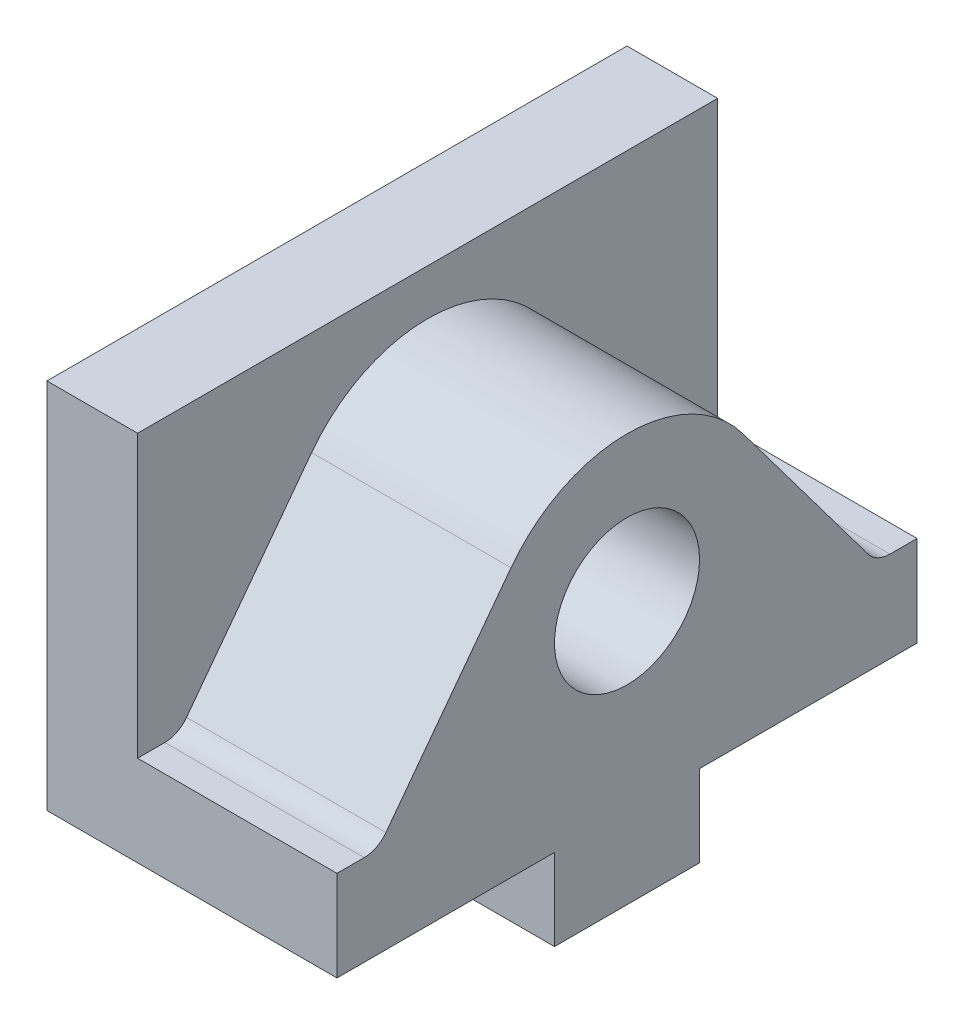
SolidWorks part; units mm, degrees
ref_plane "Front Plane" through (0, 0, 0) normal (0, 0, 1) x (1, 0, 0)
ref_plane "Top Plane" through (0, 0, 0) normal (0, 1, 0) x (1, 0, 0)
ref_plane "Right Plane" through (0, 0, 0) normal (1, 0, 0) x (0, 0, -1)
sketch "Sketch1" plane through (0, 0, 0) normal (1, 0, 0) x (0, 0, -1)
  line L0 (-32, -8) -> (32, -8)
  line L1 (-32, 18) -> (32, 18)
  line L2 (-32, 18) -> (-32, -18)
  line L3 (-32, -18) -> (32, -18)
  line L4 (32, 18) -> (32, -18)
  line L5 (-26.6, -6.8) -> (-12.8, 11.6)
  line L6 (-8, -18) -> (-8, -27)
  line L7 (26.6, -6.8) -> (12.8, 11.6)
  line L8 (-8, -27) -> (8, -27)
  line L9 (8, -27) -> (8, -18)
  circle A0 centre (0, 2) radius 16
  circle A1 centre (0, 2) radius 8
  arc A3 (-26.6, -6.8) -> (-29, -8) centre (-29, -5) cw
  arc A4 (26.6, -6.8) -> (29, -8) centre (29, -5) ccw
  point P0 (0, 0)
  point P8 (0, 2)
  point P16 (-8, -18)
  point P17 (8, -18)
  point P22 (0, -18)
  dimension "D5" = 16
  dimension "D6" = 8
  dimension "D7" = 8
  dimension "D1" = 64
  dimension "D2" = 36
  dimension "D3" = 10
  dimension "D4" = 16
  dimension "D8" = 9
extrude "Boss-Extrude2" add sketch "Sketch1" along normal blind 22 contours L8 L9 L3 L6 | A0 L0 L2 L3 L4 | L0 A0 | L5 A3 L0 A0 | A4 L7 A0 L0 | A0 L0 A1
sketch "Sketch2" plane through (0, 0, 0) normal (-1, 0, 0) x (0, 0, 1)
  line L0 (-8, -18) -> (-8, -27)
  line L1 (-32, -18) -> (32, -18)
  line L2 (-32, -18) -> (-32, 23.0518)
  line L3 (-32, 23.0518) -> (32, 23.0518)
  line L4 (32, -18) -> (32, 23.0518)
  line L5 (-8, -27) -> (8, -27)
  line L6 (8, -27) -> (8, -18)
  line M5 (-8, -27) -> (8, -27)
  line M6 (8, -27) -> (8, -18)
  line M7 (8, -18) -> (32, -18)
  line M8 (32, -18) -> (32, -8)
  line M9 (32, -8) -> (29, -8)
  arc M10 (29, -8) -> (26.6, -6.8) centre (29, -5) cw
  line M11 (26.6, -6.8) -> (12.8, 11.6)
  arc M12 (12.8, 11.6) -> (-12.8, 11.6) centre (0, 2) ccw
  line M13 (-12.8, 11.6) -> (-26.6, -6.8)
  arc M14 (-26.6, -6.8) -> (-29, -8) centre (-29, -5) cw
  line M15 (-29, -8) -> (-32, -8)
  line M16 (-32, -8) -> (-32, -18)
  line M17 (-32, -18) -> (-8, -18)
  line M18 (-8, -18) -> (-8, -27)
  circle M19 centre (0, 2) radius 8
  dimension "D1" = 64
  dimension "D2" = 41.0518
extrude "Boss-Extrude4" add sketch "Sketch2" along normal blind 10 contours L4 L3 L2 M9 M15 M14 M13 M12 M11 M10 | L1 M17 M7 M8 M9 M10 M11 M12 M13 M14 M15 M16 M19 | L1 M18 M5 M6 | M19
